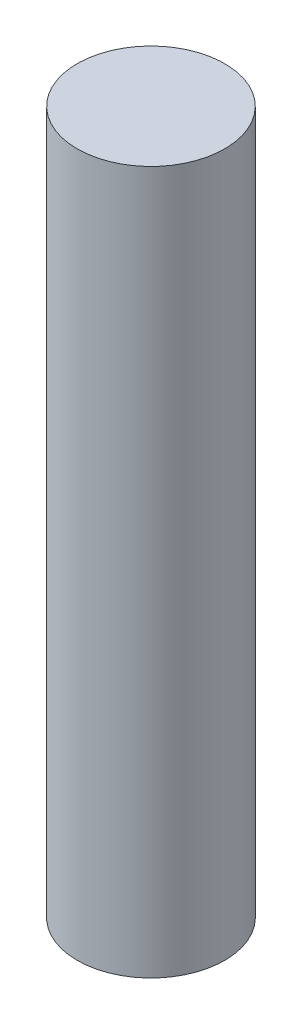
SolidWorks part; units mm, degrees
ref_plane "Front Plane" through (0, 0, 0) normal (0, 0, 1) x (1, 0, 0)
ref_plane "Top Plane" through (0, 0, 0) normal (0, 1, 0) x (1, 0, 0)
ref_plane "Right Plane" through (0, 0, 0) normal (1, 0, 0) x (0, 0, -1)
sketch "Sketch1" plane through (0, 0, 0) normal (0, 1, 0) x (1, 0, 0)
  circle A0 centre (0, 0) radius 2
  dimension "D1" = 4
extrude "Boss-Extrude1" add sketch "Sketch1" along normal blind 19.05
